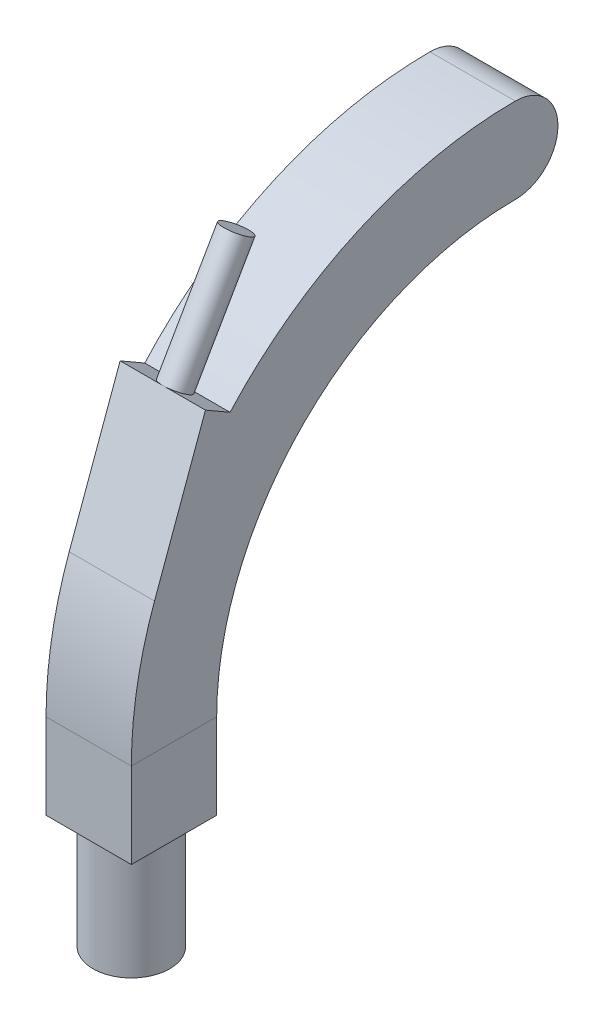
SolidWorks part; units mm, degrees
ref_plane "Front Plane" through (0, 0, 0) normal (0, 0, 1) x (1, 0, 0)
ref_plane "Top Plane" through (0, 0, 0) normal (0, 1, 0) x (1, 0, 0)
ref_plane "Right Plane" through (0, 0, 0) normal (1, 0, 0) x (0, 0, -1)
sketch "Sketch1" plane through (0, 0, 0) normal (1, 0, 0) x (0, 0, -1)
  line L0 (0, 0) -> (0, 30)
  line L1 (0, 30) -> (120, 30) construction
  line L2 (120, 30) -> (120, 150) construction
  arc A0 (120, 150) -> (0, 30) centre (120, 30) ccw
  point P5 (70.783, 100.783)
  point P7 (321.9739, 351.9739)
  dimension "D2" = 120
  dimension "D1" = 30
sketch "Sketch2" plane through (0, 0, 0) normal (0, 1, 0) x (1, 0, 0)
  line L1 (-15, -15) -> (15, -15)
  line L2 (-15, -15) -> (-15, 15)
  line L3 (-15, 15) -> (15, 15)
  line L4 (15, -15) -> (15, 15)
  line L5 (-15, -15) -> (15, 15) construction
  line L6 (-15, 15) -> (15, -15) construction
  point P0 (0, 0)
  dimension "D1" = 30
  dimension "D2" = 30
sweep "Sweep1" add profiles "Sketch2" path "Sketch1"
sketch "Sketch3" plane through (0, 0, 0) normal (0, -1, 0) x (1, 0, 0)
  circle A0 centre (0, 0) radius 13.5
  dimension "D1" = 27
extrude "Boss-Extrude1" add sketch "Sketch3" along normal blind 40
sketch "Sketch4" plane through (15, 0, 0) normal (1, 0, 0) x (0, 0, -1)
  line L0 (120, 165) -> (120, 135) construction
  line L1 (120, 165) -> (120, 135)
  arc A0 (120, 135) -> (120, 165) centre (120, 150) ccw
extrude "Boss-Extrude2" add sketch "Sketch4" against normal up to surface (30 mm away) up to face at (-15, 102.4264, -47.5736)
sketch "Sketch5" plane through (0, 0, 0) normal (1, 0, 0) x (0, 0, -1)
  line L0 (120, 165) -> (-15, 165) construction
  line L1 (-15, 165) -> (-15, 30) construction
  line L3 (19.7074, 120.3681) -> (11.0472, 125.3681)
  line L4 (11.0472, 125.3681) -> (-6.8585, 76.1727)
  arc A0 (120, 165) -> (-15, 30) centre (120, 30) ccw construction
  arc A1 (19.7074, 120.3681) -> (-6.8585, 76.1727) centre (120, 30) ccw
  dimension "D5" = 135
  dimension "D1" = 135
  dimension "D2" = 10
  dimension "D3" = 30
  dimension "D4" = 70
extrude "Boss-Extrude3" add sketch "Sketch5" along normal up to surface and the other way up to surface
sketch "Sketch6" plane through (0, 98.8096, -57.0478) normal (0, 0.866, -0.5) x (1, 0, 0)
  line L0 (0, 0) -> (0, -53.1169) construction
  line L1 (15, -53.1169) -> (-15, -53.1169) construction
  line L2 (15, -48.1169) -> (-15, -48.1169) construction
  line L3 (15, -43.1169) -> (15, -53.1169) construction
  line L4 (-15, -43.1169) -> (-15, -53.1169) construction
  circle A0 centre (0, -48.1169) radius 5
extrude "Boss-Extrude4" add sketch "Sketch6" along normal up to surface (43.0449 mm away)
